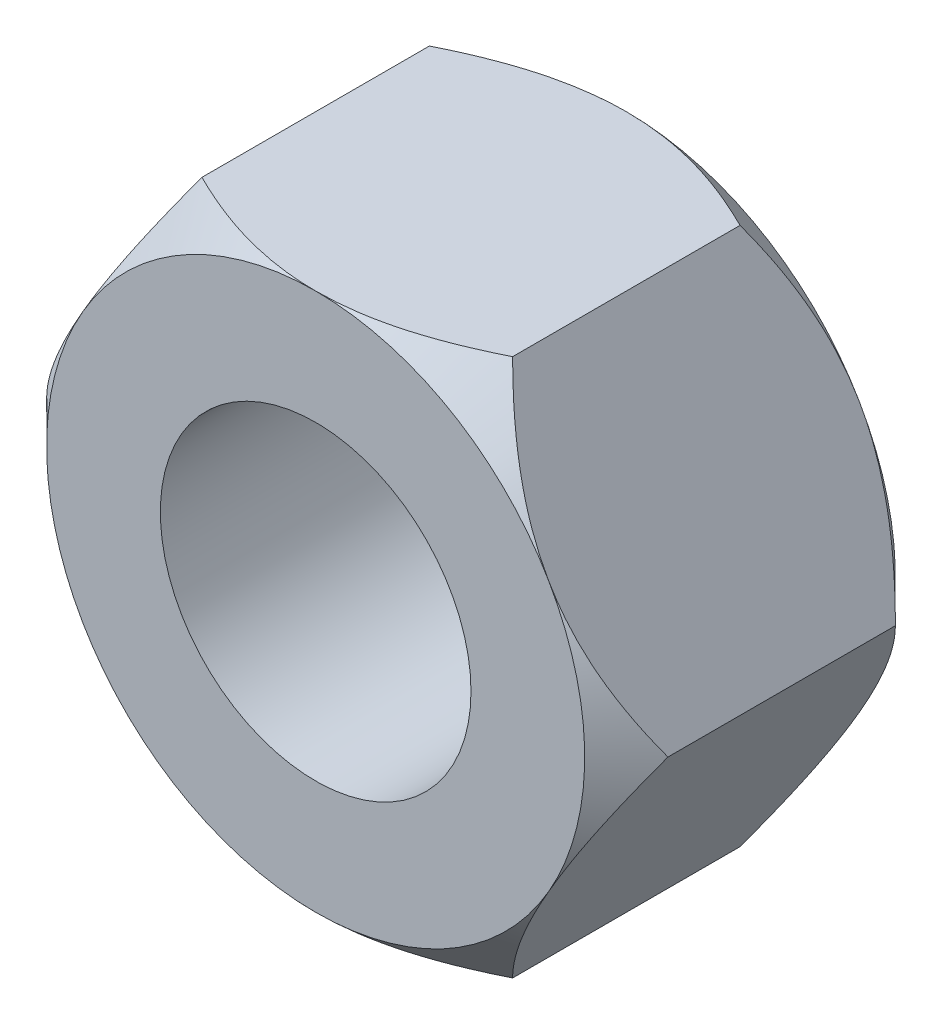
SolidWorks part; units mm, degrees
ref_plane "Front Plane" through (0, 0, 0) normal (0, 0, 1) x (1, 0, 0)
ref_plane "Top Plane" through (0, 0, 0) normal (0, 1, 0) x (1, 0, 0)
ref_plane "Right Plane" through (0, 0, 0) normal (1, 0, 0) x (0, 0, -1)
sketch "Sketch1" plane through (0, 0, 0) normal (0, 0, 1) x (1, 0, 0)
  line L1 (9, 0) -> (4.5, 7.7942)
  line L2 (4.5, 7.7942) -> (-4.5, 7.7942)
  line L3 (-4.5, 7.7942) -> (-9, 0)
  line L4 (-9, 0) -> (-4.5, -7.7942)
  line L5 (-4.5, -7.7942) -> (4.5, -7.7942)
  line L6 (4.5, -7.7942) -> (9, 0)
  circle A0 centre (0, 0) radius 7.7942 construction
  circle A1 centre (0, 0) radius 4.5
  dimension "D2" = 9
  dimension "D1" = 9
extrude "Boss-Extrude3" add sketch "Sketch1" along normal mid plane 9
sketch "Sketch3" plane through (0, 0, 4.5) normal (0, 0, 1) x (1, 0, 0)
  line L0 (-4.5, 7.7942) -> (-9, 0) construction
  circle A0 centre (0, 0) radius 7.7942
extrude "Cut-Extrude5" cut sketch "Sketch3" against normal blind 9 draft 45 flip side to cut contours A0
mirror "Mirror2" about plane through (0, 0, 0) normal (0, 0, 1) of "Cut-Extrude5"
